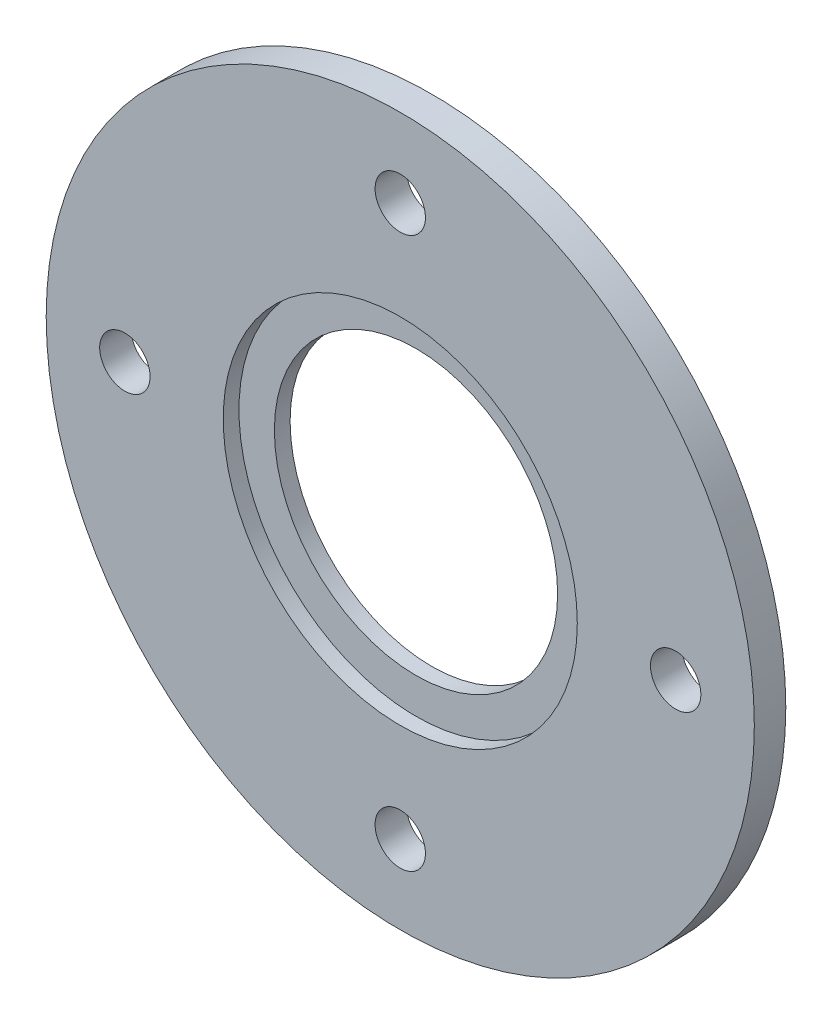
SolidWorks part; units mm, degrees
material "3.1325 (EN-AW 2017A)"
ref_plane "正面" through (0, 0, 0) normal (0, 0, 1) x (1, 0, 0)
ref_plane "平面" through (0, 0, 0) normal (0, 1, 0) x (1, 0, 0)
ref_plane "右側面" through (0, 0, 0) normal (1, 0, 0) x (0, 0, -1)
sketch "ｽｹｯﾁ1" plane through (0, 0, 0) normal (0, 0, 1) x (1, 0, 0)
  line L0 (0, 0) -> (-17.5, 0) construction
  circle A0 centre (0, 0) radius 9
  circle A1 centre (-17.5, 0) radius 1.6 construction
  circle A2 centre (0, 0) radius 22.5
  dimension "D1" = 17.5
  dimension "D2" = 18
  dimension "D3" = 3.2
  dimension "D4" = 45
extrude "ﾎﾞｽ - 押し出し1" add sketch "ｽｹｯﾁ1" along normal blind 2
sketch "ｽｹｯﾁ2" plane through (0, 0, 2) normal (0, 0, 1) x (1, 0, 0)
  circle A0 centre (-17.5, 0) radius 1.6
  circle A1 centre (-17.5, 0) radius 1.6 construction
extrude "ｶｯﾄ - 押し出し1" cut sketch "ｽｹｯﾁ2" against normal through all
pattern_circular "円形ﾊﾟﾀｰﾝ2" count 4 over 360 about axis through (0, 0, 0) along (0, 0, 1) of "ｶｯﾄ - 押し出し1"
sketch "ｽｹｯﾁ3" plane through (0, 0, 2) normal (0, 0, 1) x (1, 0, 0)
  circle A0 centre (0, 0) radius 11.25
  circle A1 centre (0, 0) radius 9
  circle A2 centre (0, 0) radius 9 construction
  dimension "D1" = 22.5
extrude "ｶｯﾄ - 押し出し2" cut sketch "ｽｹｯﾁ3" against normal blind 1
